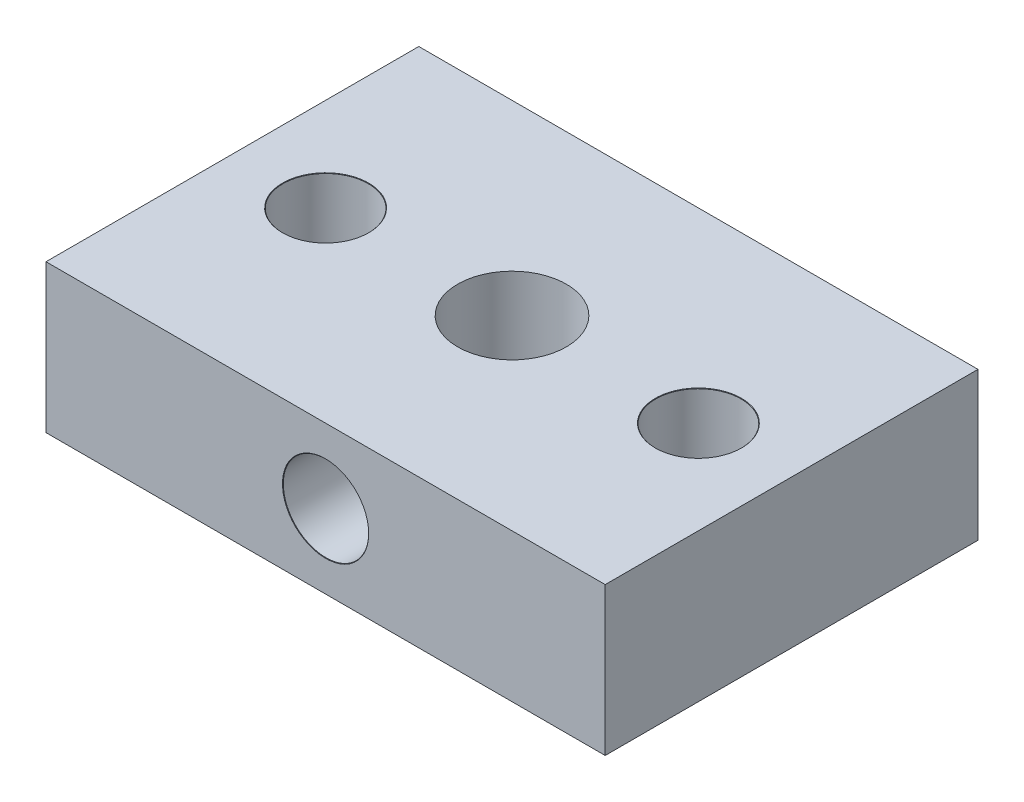
SolidWorks part; units mm, degrees
ref_plane "Front Plane" through (0, 0, 0) normal (0, 0, 1) x (1, 0, 0)
ref_plane "Top Plane" through (0, 0, 0) normal (0, 1, 0) x (1, 0, 0)
ref_plane "Right Plane" through (0, 0, 0) normal (1, 0, 0) x (0, 0, -1)
sketch "Sketch1" plane through (0, 0, 0) normal (0, 1, 0) x (1, 0, 0)
  line L1 (-18, -12) -> (18, -12)
  line L2 (-18, -12) -> (-18, 12)
  line L3 (-18, 12) -> (18, 12)
  line L4 (18, -12) -> (18, 12)
  circle A0 centre (0, 0) radius 3.5
  point P0 (0, 0)
  dimension "D1" = 36
  dimension "D5" = 7
  dimension "D2" = 24
  dimension "D3" = 12
  dimension "D4" = 18
extrude "Boss-Extrude1" add sketch "Sketch1" along normal blind 9.53
hole_wizard "M5 Clearance Hole1" positions "Sketch17" profile "Sketch3" hole size "M5" standard "ANSI Metric"
sketch "Sketch17" plane through (0, 0, 12) normal (0, 0, 1) x (1, 0, 0)
  line L0 (-18, 0) -> (18, 0) construction
  line L1 (18, 9.53) -> (18, 0) construction
  point P0 (0, 4.765)
  dimension "D1" = 4.765
  dimension "D2" = 18
sketch "Sketch3" plane through (0, 4.765, 12) normal (1, 0, 0) x (0, -1, 0)
  line L0 (0, 0) -> (0, 14.6524)
  line L1 (0, 14.6524) -> (2.75, 13)
  line L2 (2.75, 13) -> (2.75, 0.025)
  line L3 (2.75, 0.025) -> (2.775, 0)
  line L5 (2.775, 0) -> (0, 0)
  line L6 (-2.75, 0.025) -> (-2.775, 0) construction
  line L10 (0, 14.6524) -> (-2.75, 13) construction
  line L11 (0, -6.35) -> (0, 107.95) construction
  dimension "Hole Dia." = 5.5
  dimension "Hole Depth" = 13
  dimension "Near C'Sink Dia." = 5.55
  dimension "Near C'Sink Angle" = 90
  dimension "Drill Angle" = 118
hole_wizard "M5 Clearance Hole2" positions "Sketch9" profile "Sketch8" hole size "M5" standard "ANSI Metric"
sketch "Sketch9" plane through (0, 9.53, 0) normal (0, 1, 0) x (1, 0, 0)
  line L1 (-18, 12) -> (-18, -12) construction
  line L2 (18, -12) -> (18, 12) construction
  point P0 (12, 0)
  point P2 (-12, 0)
  point P7 (0, 0)
  point P9 (0, 0)
  dimension "D1" = 6
  dimension "D2" = 6
sketch "Sketch8" plane through (12, 9.53, 0) normal (1, 0, 0) x (0, 0, 1)
  line L0 (0, 0) -> (0, 14.6524)
  line L1 (0, 14.6524) -> (2.75, 13)
  line L2 (2.75, 13) -> (2.75, 0.025)
  line L3 (2.75, 0.025) -> (2.775, 0)
  line L5 (2.775, 0) -> (0, 0)
  line L6 (-2.75, 0.025) -> (-2.775, 0) construction
  line L10 (0, 14.6524) -> (-2.75, 13) construction
  line L11 (0, -6.35) -> (0, 107.95) construction
  dimension "Hole Dia." = 5.5
  dimension "Hole Depth" = 13
  dimension "Near C'Sink Dia." = 5.55
  dimension "Near C'Sink Angle" = 90
  dimension "Drill Angle" = 118
thread "Thread1" pitch 0.8 start angle 0, offset 0, length 10, pitch 0.8, diameter 5.5
ref_plane "Plane1" through (-2.75, 4.765, 12) normal (0, -1, 0) x (-1, 0, 0)
sketch "Thread Profile1" plane through (-2.75, 4.765, 12) normal (0, -1, 0) x (-1, 0, 0)
  line L0 (0, 0) -> (0, 0.8) construction
  line L1 (0, 0) -> (0.433, 0.25)
  line L2 (0.433, 0.25) -> (0.433, 0.35)
  line L3 (0.433, 0.35) -> (0, 0.6)
  line L4 (0.433, 0.3) -> (0, 0.3) construction
  line L11 (0, 0) -> (0, 0.6)
  point P2 (0, 0)
  dimension "Pitch" = 0.8
  dimension "Profile_Angle" = 60
  dimension "Profile_Land" = 0.1
  dimension "Profile_Height" = 0.433
